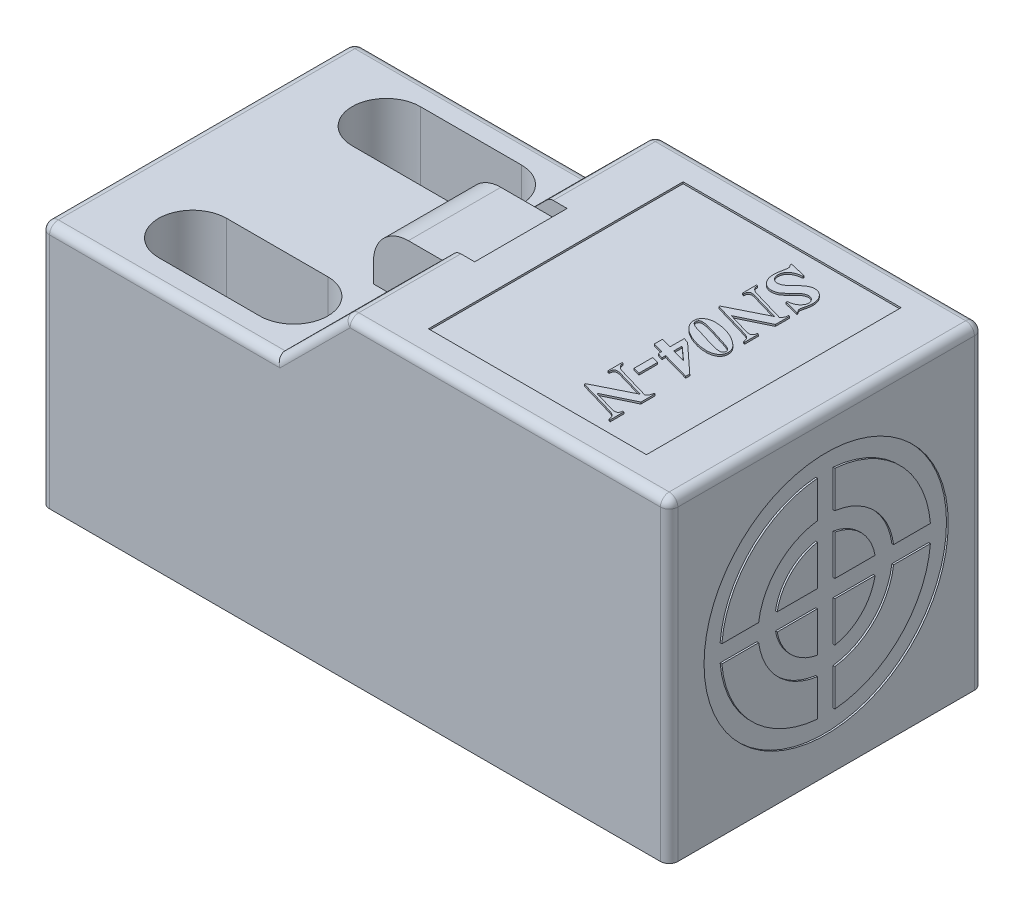
SolidWorks part; units mm, degrees
ref_plane "Спереди" through (0, 0, 0) normal (0, 0, 1) x (1, 0, 0)
ref_plane "Сверху" through (0, 0, 0) normal (0, 1, 0) x (1, 0, 0)
ref_plane "Справа" through (0, 0, 0) normal (1, 0, 0) x (0, 0, -1)
sketch "Sketch1" plane through (0, 0, 0) normal (0, 0, 1) x (1, 0, 0)
  line L1 (-66.9468, 32.4792) -> (-48.4468, 32.4792)
  line L2 (-84.4668, 28.4792) -> (-84.4668, 14.3792)
  line L3 (-84.4668, 14.3792) -> (-48.4468, 14.3792)
  line L4 (-48.4468, 32.4792) -> (-48.4468, 14.3792)
  line L5 (-70.9668, 28.4792) -> (-84.4668, 28.4792)
  line L7 (-70.9668, 28.4792) -> (-66.9468, 32.4792)
  dimension "D2" = 18.1
  dimension "D3" = 14.1
extrude "Extrude1" add sketch "Sketch1" along normal blind 18
sketch "Sketch2" plane through (0, 28.4792, 0) normal (0, 1, 0) x (1, 0, 0)
  line L0 (-79.2168, -14.55) -> (-73.4168, -14.55) construction
  line L1 (-79.2168, -12.6) -> (-73.4168, -12.6)
  line L2 (-79.2168, -16.5) -> (-73.4168, -16.5)
  line L3 (-84.4668, -18) -> (-84.4668, 0) construction
  line L4 (-70.9668, -18) -> (-84.4668, -18) construction
  arc A0 (-79.2168, -12.6) -> (-79.2168, -16.5) centre (-79.2168, -14.55) ccw
  arc A1 (-73.4168, -16.5) -> (-73.4168, -12.6) centre (-73.4168, -14.55) ccw
  point P2 (-76.3168, -14.55)
  dimension "D1" = 5.8
  dimension "D3" = 5.25
  dimension "D2" = 3.9
  dimension "D4" = 1.5
extrude "Extrude2" cut sketch "Sketch2" against normal blind 17.9
pattern_linear "LPattern1" count 2 spacing 11.1 along (0, 0, -1) of "Extrude2"
sketch "Sketch3" plane through (0, 28.4792, 0) normal (0, 1, 0) x (1, 0, 0)
  line L0 (-48.4468, -18) -> (-48.4468, 0) construction
  line L1 (-71.7468, -6.35) -> (-65.9468, -6.35)
  line L2 (-71.7468, -6.35) -> (-71.7468, -11.65)
  line L3 (-71.7468, -11.65) -> (-65.9468, -11.65)
  line L4 (-65.9468, -6.35) -> (-65.9468, -11.65)
  line L5 (-48.4468, -18) -> (-66.9468, -18) construction
  dimension "D1" = 5.3
  dimension "D2" = 5.8
  dimension "D3" = 17.5
  dimension "D4" = 6.35
extrude "Extrude3" add sketch "Sketch3" along normal blind 5
sketch "Sketch4" plane through (0, 33.4792, 0) normal (0, 1, 0) x (1, 0, 0)
  line L0 (-65.9468, -11.65) -> (-65.9468, -6.35) construction
  line L1 (-71.7468, -6.35) -> (-65.9468, -6.35)
  line L2 (-71.7468, -6.35) -> (-71.7468, -11.65)
  line L3 (-71.7468, -11.65) -> (-65.9468, -11.65)
  line L4 (-65.9468, -6.35) -> (-65.9468, -11.65)
extrude "Extrude4" cut sketch "Sketch4" against normal blind 1.85
fillet "Fillet1" radius 2 1 edges at (-71.7468, 31.6292, 9)
sketch "Sketch5" plane through (-84.4668, 0, 0) normal (-1, 0, 0) x (0, 0, 1)
  line L0 (18, 14.3792) -> (0, 14.3792) construction
  line L1 (5, 14.3792) -> (13, 14.3792)
  line L2 (5, 14.3792) -> (5, 20.3892)
  line L3 (8.99, 24.3792) -> (9.01, 24.3792)
  line L4 (13, 14.3792) -> (13, 20.3892)
  line L5 (0, 28.4792) -> (0, 14.3792) construction
  arc A0 (9.01, 24.3792) -> (13, 20.3892) centre (9.01, 20.3892) cw
  arc A1 (5, 20.3892) -> (8.99, 24.3792) centre (8.99, 20.3892) cw
  point P10 (13, 24.3792)
  point P13 (5, 24.3792)
  dimension "D4" = 3.99
  dimension "D1" = 8
  dimension "D2" = 5
  dimension "D3" = 10
extrude "Extrude5" add sketch "Sketch5" along normal blind 1.2
sketch "Sketch6" plane through (-85.6668, 0, 0) normal (-1, 0, 0) x (0, 0, 1)
  circle A0 centre (8.99, 20.3892) radius 1.6
extrude "Extrude6" add sketch "Sketch6" along normal blind 1
sketch "Sketch7" plane through (0, 32.4792, 0) normal (0, 1, 0) x (1, 0, 0)
  line L0 (-48.4468, 0) -> (-66.9468, 0) construction
  line L1 (-63.9468, -1.7) -> (-51.4468, -1.7)
  line L2 (-63.9468, -1.7) -> (-63.9468, -16.3)
  line L3 (-63.9468, -16.3) -> (-51.4468, -16.3)
  line L4 (-51.4468, -1.7) -> (-51.4468, -16.3)
  line L5 (-48.4468, -18) -> (-66.9468, -18) construction
  line L6 (-48.4468, -18) -> (-48.4468, 0) construction
  line L7 (-66.9468, -6.35) -> (-66.9468, 0) construction
  dimension "D1" = 1.7
  dimension "D2" = 1.7
  dimension "D3" = 3
  dimension "D4" = 3
extrude "Extrude7" cut sketch "Sketch7" against normal blind 0.1
sketch "Sketch8" plane through (-48.4468, 0, 0) normal (1, 0, 0) x (0, 0, -1)
  line L0 (-9.5, 26.235) -> (-9.5, 23.9292)
  line L1 (-14.9791, 23.9292) -> (-12.8678, 23.9292)
  line L2 (-8.5, 26.235) -> (-8.5, 23.9292)
  line L3 (-9.5, 29.4084) -> (-9.5, 27.2971)
  line L4 (-8.5, 29.4084) -> (-8.5, 27.2971)
  line L5 (-5.1322, 23.9292) -> (-3.0209, 23.9292)
  line L8 (-5.1322, 22.9292) -> (-3.0209, 22.9292)
  line L9 (-8.5, 23.9292) -> (-6.1942, 23.9292)
  line L10 (-14.9791, 22.9292) -> (-12.8678, 22.9292)
  line L11 (-9.5, 22.9292) -> (-9.5, 20.6234)
  line L13 (-8.5, 22.9292) -> (-8.5, 20.6234)
  line L15 (-8.5, 22.9292) -> (-6.1942, 22.9292)
  line L17 (-9.5, 19.5614) -> (-9.5, 17.4501)
  line L19 (-8.5, 19.5614) -> (-8.5, 17.4501)
  line L20 (-11.8058, 22.9292) -> (-9.5, 22.9292)
  line L21 (-11.8058, 23.9292) -> (-9.5, 23.9292)
  circle A0 centre (-9, 23.4292) radius 7
  arc A1 (-14.9791, 22.9292) -> (-9.5, 17.4501) centre (-9, 23.4292) ccw
  arc A2 (-8.5, 19.5614) -> (-5.1322, 22.9292) centre (-9, 23.4292) ccw
  arc A3 (-8.5, 20.6234) -> (-6.1942, 22.9292) centre (-9, 23.4292) ccw
  arc A4 (-11.8058, 22.9292) -> (-9.5, 20.6234) centre (-9, 23.4292) ccw
  arc A5 (-12.8678, 22.9292) -> (-9.5, 19.5614) centre (-9, 23.4292) ccw
  arc A6 (-9.5, 29.4084) -> (-14.9791, 23.9292) centre (-9, 23.4292) ccw
  arc A7 (-9.5, 27.2971) -> (-12.8678, 23.9292) centre (-9, 23.4292) ccw
  arc A8 (-9.5, 26.235) -> (-11.8058, 23.9292) centre (-9, 23.4292) ccw
  arc A9 (-6.1942, 23.9292) -> (-8.5, 26.235) centre (-9, 23.4292) ccw
  arc A10 (-5.1322, 23.9292) -> (-8.5, 27.2971) centre (-9, 23.4292) ccw
  arc A11 (-3.0209, 23.9292) -> (-8.5, 29.4084) centre (-9, 23.4292) ccw
  arc A12 (-8.5, 17.4501) -> (-3.0209, 22.9292) centre (-9, 23.4292) ccw
  point P5 (-9, 30.4292)
  point P6 (-9, 16.4292)
  point P7 (-16, 23.4292)
  point P8 (-2, 23.4292)
  point P9 (-9.5, 30.4292)
  point P10 (-9.5, 16.4292)
  point P11 (-16, 22.9292)
  point P12 (-2, 22.9292)
  point P13 (-8.5, 30.4292)
  point P14 (-8.5, 16.4292)
  point P15 (-16, 23.9292)
  point P16 (-2, 23.9292)
extrude "Extrude8" cut sketch "Sketch8" against normal blind 0.1
fillet "Fillet3" radius 0.5 14 edges at (-66.9468, 32.4792, 3.175) (-66.9468, 32.4792, 14.825) (-57.6968, 32.4792, 18) (-68.9568, 30.4792, 18) (-77.7168, 28.4792, 18) (-84.4668, 21.4292, 18) (-48.4468, 23.4292, 18) (-84.4668, 28.4792, 9) (-84.4668, 21.4292, 0) (-77.7168, 28.4792, 0) (-68.9568, 30.4792, 0) (-48.4468, 23.4292, 0) (-48.4468, 32.4792, 9) (-57.6968, 32.4792, 0)
sketch "Sketch12" plane through (0, 32.3792, 0) normal (0, 1, 0) x (-1, 0, 0)
  text T0 "\r\n<b><i>SN04-N</i></b>" font "Times New Roman" height 2.5
extrude "Extrude10" add sketch "Sketch12" along normal blind 0.1
